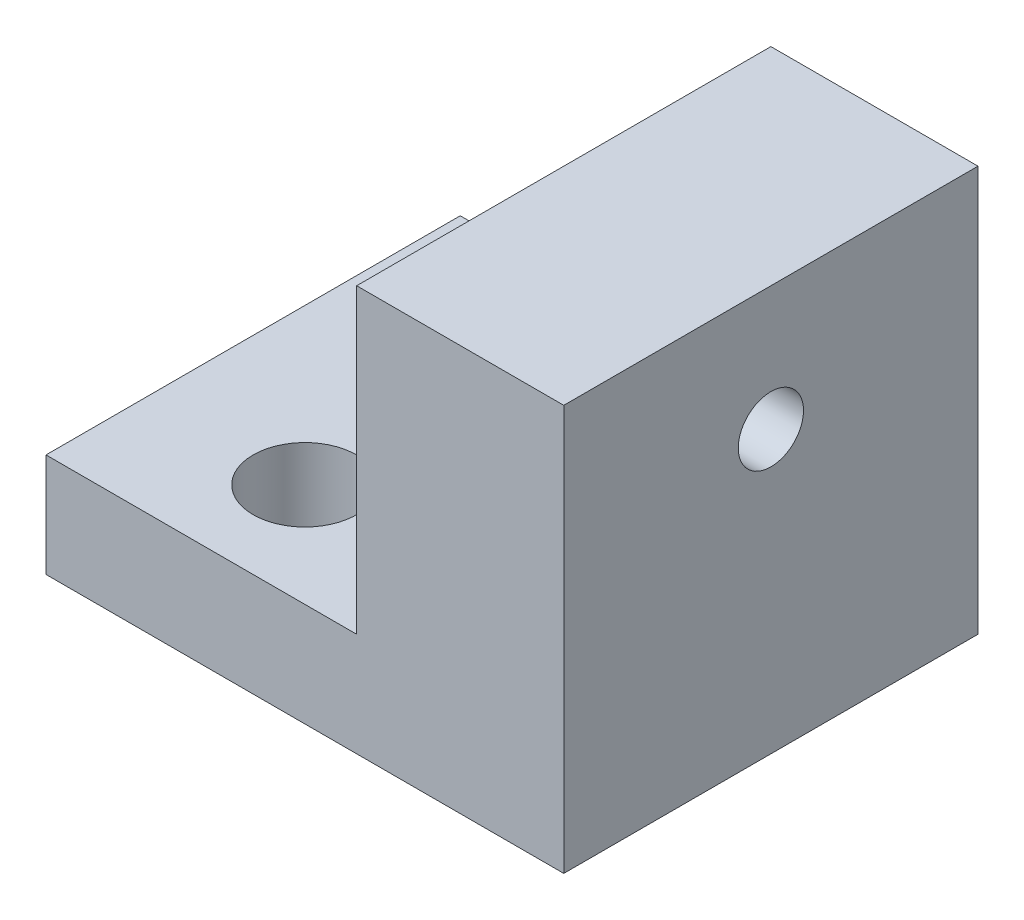
SolidWorks part; units mm, degrees
ref_plane "Front Plane" through (0, 0, 0) normal (0, 0, 1) x (1, 0, 0)
ref_plane "Top Plane" through (0, 0, 0) normal (0, 1, 0) x (1, 0, 0)
ref_plane "Right Plane" through (0, 0, 0) normal (1, 0, 0) x (0, 0, -1)
sketch "Sketch1" plane through (0, 0, 0) normal (0, 0, 1) x (1, 0, 0)
  line L1 (6.35, -19.05) -> (-6.35, -19.05)
  line L2 (6.35, -19.05) -> (6.35, 19.05)
  line L3 (6.35, 19.05) -> (-6.35, 19.05)
  line L4 (-6.35, -19.05) -> (-6.35, 19.05)
  line L5 (6.35, -19.05) -> (-6.35, 19.05) construction
  line L6 (6.35, 19.05) -> (-6.35, -19.05) construction
  line L7 (-6.35, -19.05) -> (-25.4, -19.05)
  line L8 (-6.35, -19.05) -> (-6.35, -12.7)
  line L9 (-6.35, -12.7) -> (-25.4, -12.7)
  line L10 (-25.4, -19.05) -> (-25.4, -12.7)
  point P0 (0, 0)
  dimension "D1" = 6.35
  dimension "D2" = 19.05
  dimension "D3" = 12.7
  dimension "D4" = 38.1
extrude "Boss-Extrude1" add sketch "Sketch1" along normal blind 25.4 contours L10 L7 L4 L9 | L4 L1 L2 L3
sketch "Sketch2" plane through (0, -12.7, 0) normal (0, 1, 0) x (1, 0, 0)
  line L0 (-15.875, -19.05) -> (-15.875, -6.35) construction
  line L1 (-25.4, -25.4) -> (-25.4, 0) construction
  line L2 (-6.35, 0) -> (-25.4, 0) construction
  circle A0 centre (-15.875, -6.35) radius 3.175
  circle A1 centre (-15.875, -19.05) radius 3.175
  point P6 (-25.4, -12.7)
  point P7 (-15.875, -12.7)
  point P8 (-15.3928, -31.9316)
  point P11 (-15.875, 0)
  dimension "D1" = 6.35
  dimension "D2" = 6.35
extrude "Cut-Extrude1" cut sketch "Sketch2" against normal up to next
sketch "Sketch3" plane through (6.35, 0, 0) normal (1, 0, 0) x (0, 0, -1)
  line L0 (-25.4, 19.05) -> (0, 19.05) construction
  line L1 (-25.4, -19.05) -> (0, -19.05) construction
  circle A0 centre (-12.7, -1.811) radius 2
  point P4 (-12.7, 19.05)
  dimension "D1" = 4
  dimension "D2" = 17.239
extrude "Cut-Extrude2" cut sketch "Sketch3" against normal up to next
sketch "Sketch4" plane through (6.35, 0, 0) normal (1, 0, 0) x (0, 0, -1)
  line L0 (0, -19.05) -> (0, 19.05) construction
  line L1 (-25.4, 19.05) -> (0, 19.05)
  line L2 (-25.4, 19.05) -> (-25.4, 5.809)
  line L3 (-25.4, 5.809) -> (0, 5.809)
  line L4 (0, 19.05) -> (0, 5.809)
  circle A0 centre (-12.7, -1.811) radius 2 construction
  dimension "D1" = 7.62
extrude "Cut-Extrude3" cut sketch "Sketch4" against normal up to next
